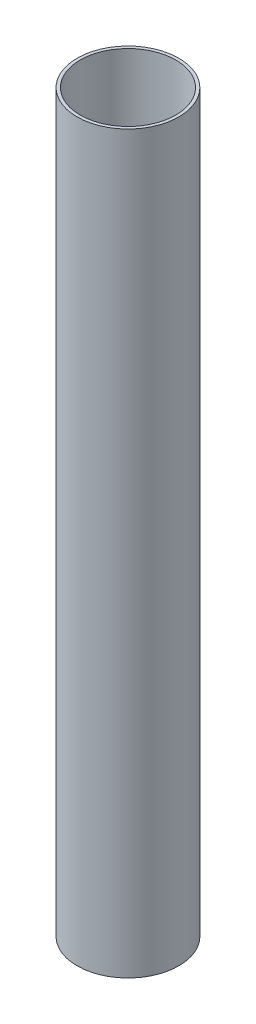
SolidWorks part; units mm, degrees
ref_plane "Front Plane" through (0, 0, 0) normal (0, 0, 1) x (1, 0, 0)
ref_plane "Top Plane" through (0, 0, 0) normal (0, 1, 0) x (1, 0, 0)
ref_plane "Right Plane" through (0, 0, 0) normal (1, 0, 0) x (0, 0, -1)
sketch "Sketch1" plane through (0, 0, 0) normal (0, 0, 1) x (1, 0, 0)
  line L1 (49.53, 762) -> (52.705, 762)
  line L2 (49.53, 762) -> (49.53, 0)
  line L3 (49.53, 0) -> (52.705, 0)
  line L4 (52.705, 762) -> (52.705, 0)
  dimension "D1" = 0
  dimension "D2" = 49.53
  dimension "D3" = 3.175
  dimension "D4" = 762
ref_axis "Central Axis" through (0, 797.9133, 0) along (0, -1, 0)
revolve "Revolve1" add sketch "Sketch1" angle 360 about axis through (0, 797.9133, 0) along (0, -1, 0)
ref_plane "fin plane 1" through (0, 0, 0) normal (-0.866, 0, 0.5) x (0, -1, 0)
ref_plane "fin plane 2" through (0, 0, 0) normal (0.866, 0, 0.5) x (0, -1, 0)
